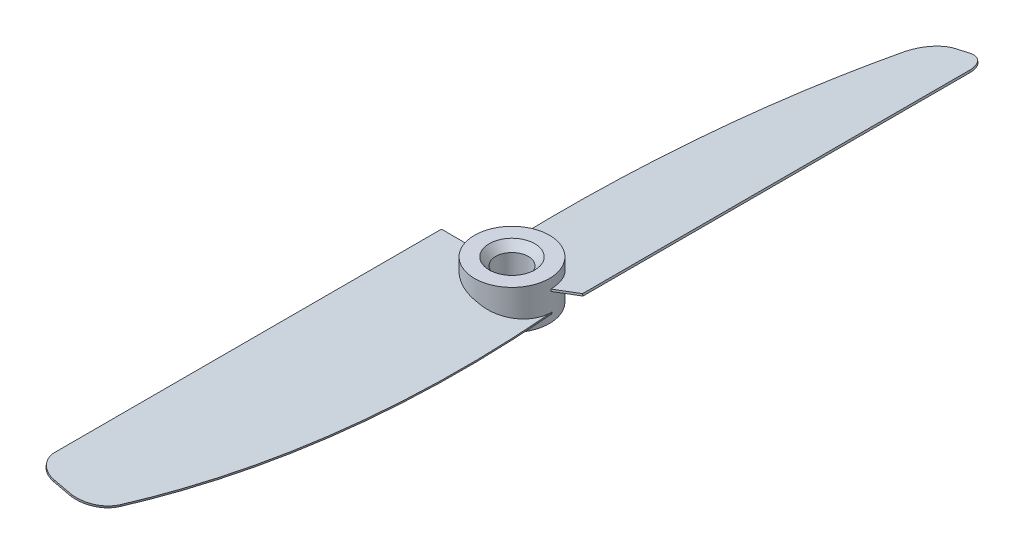
SolidWorks part; units mm, degrees
ref_plane "Front Plane" through (0, 0, 0) normal (0, 0, 1) x (1, 0, 0)
ref_plane "Top Plane" through (0, 0, 0) normal (0, 1, 0) x (1, 0, 0)
ref_plane "Right Plane" through (0, 0, 0) normal (1, 0, 0) x (0, 0, -1)
sketch "Sketch2" plane through (0, 0, 0) normal (0, 1, 0) x (1, 0, 0)
  circle A0 centre (0, 0) radius 5.75
  dimension "D1" = 11.5
extrude "Boss-Extrude1" add sketch "Sketch2" along normal mid plane 6
sketch "Sketch3" plane through (0, 0, 0) normal (0, 0, 1) x (1, 0, 0)
  line L0 (-5.75, 1.3275) -> (5.75, -1.3275) construction
  line L1 (-5.75, 3) -> (-5.75, -3) construction
  line L2 (5.75, -3) -> (5.75, 3) construction
  line L3 (-5.75, -3) -> (5.75, -3) construction
  dimension "D1" = 13
ref_plane "Plane1" through (0, 0, 0) normal (-0.225, -0.9744, 0) x (0.9744, -0.225, 0)
sketch "Sketch4" plane through (0, 0, 0) normal (-0.225, -0.9744, 0) x (0.9744, -0.225, 0)
  line L0 (-4.9278, 0) -> (-9.991, 1.1247)
  line L1 (-9.991, 1.1247) -> (-9.991, 60.5)
  line L2 (-6.991, 63.5) -> (-4.2157, 63.5)
  arc A0 (0.0154, 60.1047) -> (-4.2157, 63.5) centre (-4.729, 58.5264) ccw
  arc A1 (-9.991, 60.5) -> (-6.991, 63.5) centre (-6.991, 60.5) cw
  ellipse E0 centre (0.6749, 0) end of major axis (0.6749, 5.75) minor radius 5.6026 construction
  ellipse E1 centre (0.6749, 0) end of major axis (0.6749, 5.75) minor radius 5.6026 (6.2775, 0) -> (-4.9278, 0) ccw
  spline S0 degree 3 poles (6.2775, 0) (7.696, 19.9706) (6.3608, 41.0308) (0.0154, 60.1047) knots 0 0 0 0 0.936919 0.936919 0.936919 0.936919
  point P19 (-4.2157, 63.5)
  dimension "D2" = 5
  dimension "D1" = 3
  dimension "D3" = 63.5
extrude "Boss-Extrude2" add sketch "Sketch4" along normal mid plane 0.3
pattern_circular "CirPattern1" count 2 over 360 about axis through (0, 3, 0) along (0, -1, 0) of "Boss-Extrude2"
sketch "Sketch5" plane through (0, 3, 0) normal (0, 1, 0) x (1, 0, 0)
  circle A0 centre (0, 0) radius 2.5
  dimension "D1" = 5
extrude "Cut-Extrude1" cut sketch "Sketch5" against normal through all
chamfer "Chamfer1" distance 1 angle 50 2 edges at (0, 3, 2.5) (0, -3, 2.5)
